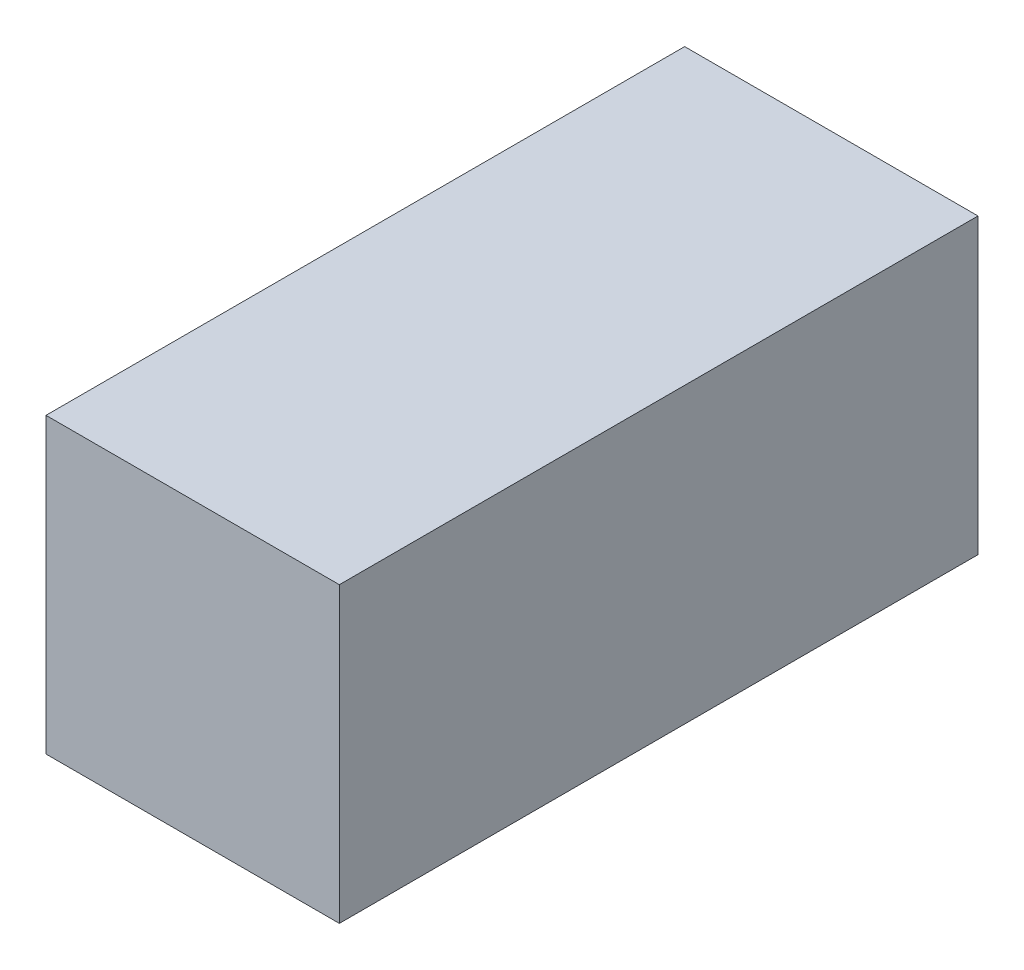
SolidWorks part; units mm, degrees
material "Plain Carbon Steel"
ref_plane "Front Plane" through (0, 0, 0) normal (0, 0, 1) x (1, 0, 0)
ref_plane "Top Plane" through (0, 0, 0) normal (0, 1, 0) x (1, 0, 0)
ref_plane "Right Plane" through (0, 0, 0) normal (1, 0, 0) x (0, 0, -1)
sketch "Sketch1" plane through (0, 0, 0) normal (0, 0, 1) x (1, 0, 0)
  line L1 (0, 0) -> (35, 0)
  line L2 (0, 0) -> (0, 35)
  line L3 (0, 35) -> (35, 35)
  line L4 (35, 0) -> (35, 35)
  dimension "D1" = 35
  dimension "D2" = 35
extrude "Boss-Extrude1" add sketch "Sketch1" along normal blind 76.2
